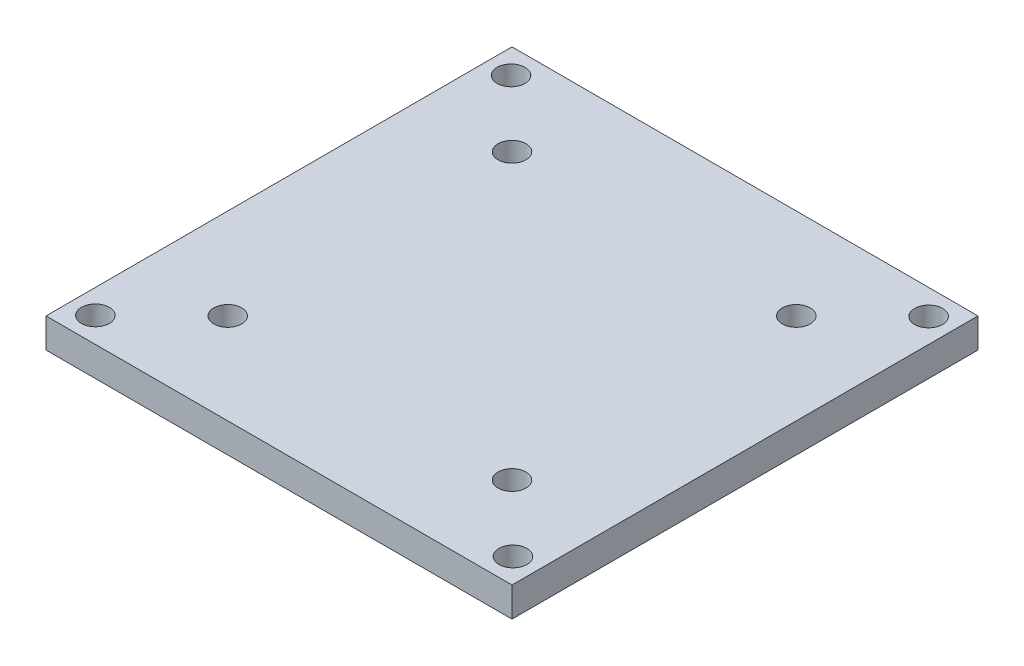
SolidWorks part; units mm, degrees
material "Acrylic (Medium-high impact)"
ref_plane "Front Plane" through (0, 0, 0) normal (0, 0, 1) x (1, 0, 0)
ref_plane "Top Plane" through (0, 0, 0) normal (0, 1, 0) x (1, 0, 0)
ref_plane "Right Plane" through (0, 0, 0) normal (1, 0, 0) x (0, 0, -1)
sketch "Sketch1" plane through (0, 0, 0) normal (0, 1, 0) x (1, 0, 0)
  line L1 (25, 25) -> (-25, 25)
  line L2 (25, 25) -> (25, -25)
  line L3 (25, -25) -> (-25, -25)
  line L4 (-25, 25) -> (-25, -25)
  line L5 (25, 25) -> (-25, -25) construction
  line L6 (25, -25) -> (-25, 25) construction
  line L7 (22.4, 22.3) -> (-22.4, 22.3) construction
  line L8 (22.4, 22.3) -> (22.4, -22.3) construction
  line L9 (22.4, -22.3) -> (-22.4, -22.3) construction
  line L10 (-22.4, 22.3) -> (-22.4, -22.3) construction
  line L11 (22.4, 22.3) -> (-22.4, -22.3) construction
  line L12 (22.4, -22.3) -> (-22.4, 22.3) construction
  line L13 (15.25, -15.25) -> (-15.25, -15.25) construction
  line L14 (15.25, -15.25) -> (15.25, 15.25) construction
  line L15 (15.25, 15.25) -> (-15.25, 15.25) construction
  line L16 (-15.25, -15.25) -> (-15.25, 15.25) construction
  line L17 (15.25, -15.25) -> (-15.25, 15.25) construction
  line L18 (15.25, 15.25) -> (-15.25, -15.25) construction
  circle A0 centre (-22.4, 22.3) radius 1.5
  circle A1 centre (22.4, 22.3) radius 1.5
  circle A2 centre (22.4, -22.3) radius 1.5
  circle A3 centre (-22.4, -22.3) radius 1.5
  circle A4 centre (-15.25, 15.25) radius 1.5
  circle A5 centre (15.25, 15.25) radius 1.5
  circle A6 centre (15.25, -15.25) radius 1.5
  circle A7 centre (-15.25, -15.25) radius 1.5
  point P0 (0, 0)
  point P6 (0, 0)
  point P12 (0, 0)
  dimension "D5" = 3
  dimension "D10" = 2
  dimension "D1" = 50
  dimension "D2" = 50
  dimension "D3" = 44.6
  dimension "D4" = 44.8
  dimension "D8" = 30.5
  dimension "D9" = 30.5
  dimension "D6" = 2
  dimension "D7" = 2
  dimension "D11" = 2
extrude "Boss-Extrude1" add sketch "Sketch1" along normal blind 3.175 contours L1 L4 L3 L2 A7 A6 A5 A4 A3 A2 A1 A0 | L8 L7 L10 L9
